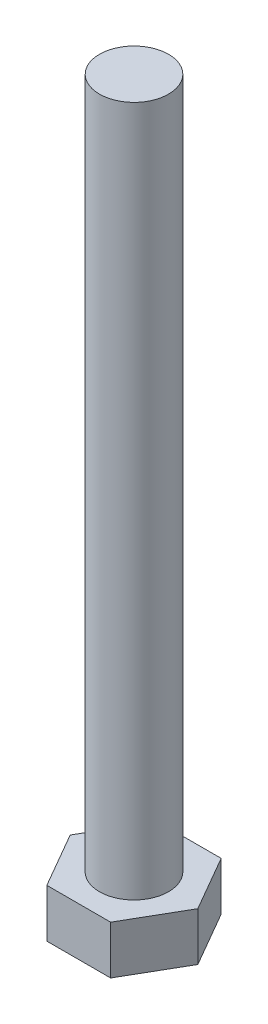
SolidWorks part; units mm, degrees
ref_plane "Front Plane" through (0, 0, 0) normal (0, 0, 1) x (1, 0, 0)
ref_plane "Top Plane" through (0, 0, 0) normal (0, 1, 0) x (1, 0, 0)
ref_plane "Right Plane" through (0, 0, 0) normal (1, 0, 0) x (0, 0, -1)
sketch "Sketch1" plane through (0, 0, 0) normal (0, 1, 0) x (1, 0, 0)
  line L1 (4.6188, 0) -> (2.3094, 4)
  line L2 (2.3094, 4) -> (-2.3094, 4)
  line L3 (-2.3094, 4) -> (-4.6188, 0)
  line L4 (-4.6188, 0) -> (-2.3094, -4)
  line L5 (-2.3094, -4) -> (2.3094, -4)
  line L6 (2.3094, -4) -> (4.6188, 0)
  circle A0 centre (0, 0) radius 4 construction
  dimension "D1" = 8
extrude "Boss-Extrude1" add sketch "Sketch1" along normal blind 3.5
sketch "Sketch2" plane through (0, 3.5, 0) normal (0, 1, 0) x (1, 0, 0)
  circle A0 centre (0, 0) radius 2.5
  dimension "D1" = 5
extrude "Boss-Extrude2" add sketch "Sketch2" along normal blind 50
cosmetic thread "Cosmetic Thread1" [suppressed] parameters "D2"=4.11
cosmetic thread "Cosmetic Thread2" [suppressed] parameters "D2"=4.11
